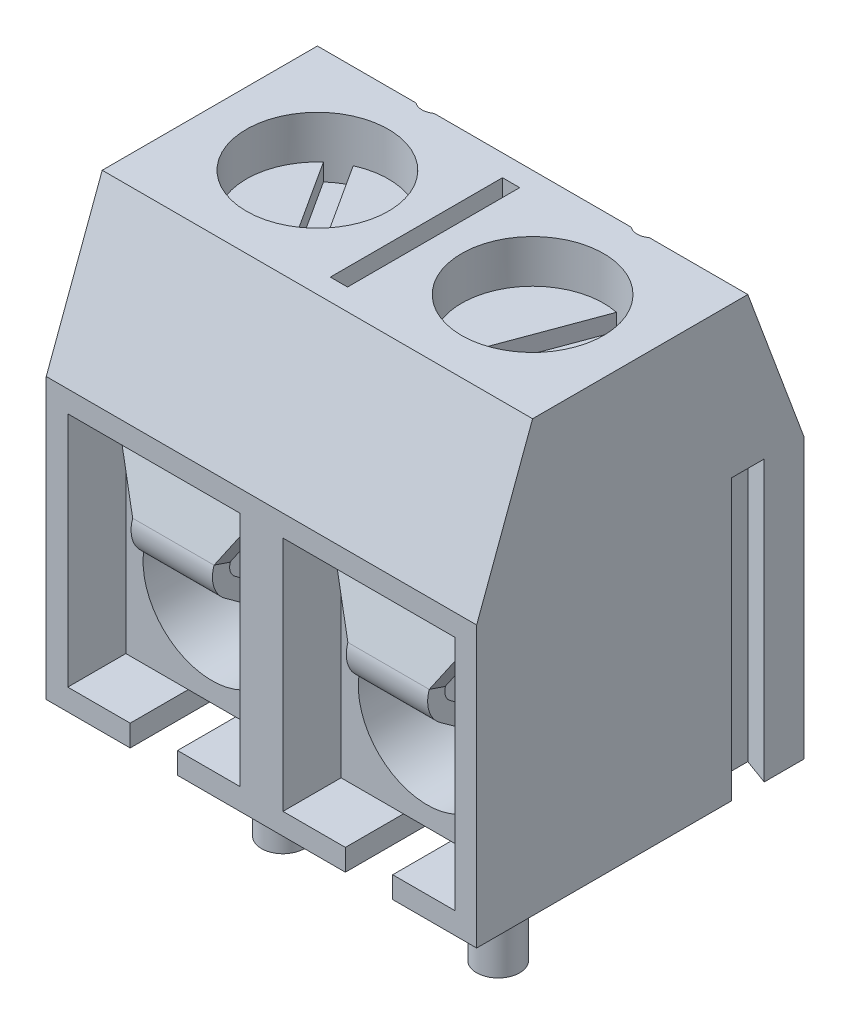
SolidWorks part; units mm, degrees
ref_plane "Front Plane" through (0, 0, 0) normal (0, 0, 1) x (1, 0, 0)
ref_plane "Top Plane" through (0, 0, 0) normal (0, 1, 0) x (1, 0, 0)
ref_plane "Right Plane" through (0, 0, 0) normal (1, 0, 0) x (0, 0, -1)
sketch "Sketch1" plane through (0, 0, 0) normal (0, 1, 0) x (1, 0, 0)
  line L1 (-5, 3.8) -> (5, 3.8)
  line L2 (-5, 3.8) -> (-5, -3.8)
  line L3 (-5, -3.8) -> (5, -3.8)
  line L4 (5, 3.8) -> (5, -3.8)
  dimension "D1" = 10
  dimension "D2" = 5
  dimension "D3" = 7.6
  dimension "D4" = 3.8
extrude "Extrude1" add sketch "Sketch1" along normal blind 10
sketch "Sketch2" plane through (0, 0, 0) normal (1, 0, 0) x (0, 0, -1)
  line L0 (2.5, 10) -> (3.8, 6.5)
  line L1 (3.8, 10) -> (-3.8, 10) construction
  line L2 (3.8, 10) -> (3.8, 0) construction
  line L3 (3.8, 6.5) -> (-3.8, 6.5) construction
  line L4 (-3.8, 10) -> (-3.8, 0) construction
  line L5 (-3.8, 6.5) -> (-2.5, 10)
  line L6 (-2.5, 10) -> (2.5, 10)
  line L7 (3.8, 6.5) -> (3.8, 0)
  line L8 (3.8, 0) -> (-3.8, 0)
  line L9 (-3.8, 0) -> (-3.8, 6.5)
  dimension "D1" = 5
  dimension "D2" = 2.5
  dimension "D3" = 3.5
extrude "Cut-Extrude1" cut sketch "Sketch2" against normal through all and the other way through all flip side to cut
sketch "Sketch3" plane through (0, 10, 0) normal (0, 1, 0) x (-1, 0, 0)
  line L0 (5, -2.5) -> (-5, -2.5) construction
  line L1 (0.2, -2) -> (-0.2, -2)
  line L2 (0.2, -2) -> (0.2, 2)
  line L3 (0.2, 2) -> (-0.2, 2)
  line L4 (-0.2, -2) -> (-0.2, 2)
  circle A0 centre (2.5, 0) radius 1.65
  circle A1 centre (-2.5, 0) radius 1.65
  circle A2 centre (2.5, -2.78) radius 0.35
  circle A3 centre (-2.5, -2.78) radius 0.35
  dimension "D7" = 3.3
  dimension "D8" = 0.7
  dimension "D1" = 0.4
  dimension "D2" = 0.2
  dimension "D3" = 4
  dimension "D4" = 2
  dimension "D5" = 2.5
  dimension "D6" = 2.5
  dimension "D9" = 0.28
extrude "Cut-Extrude2" cut sketch "Sketch3" against normal blind 4
sketch "Sketch4" plane through (0, 0, 3.8) normal (0, 0, 1) x (1, 0, 0)
  line L0 (-5, 6.5) -> (-5, 0) construction
  line L1 (-4.5, 6) -> (-0.5, 6)
  line L2 (-4.5, 6) -> (-4.5, 0.5)
  line L3 (-4.5, 0.5) -> (-0.5, 0.5)
  line L4 (-0.5, 6) -> (-0.5, 0.5)
  line L5 (0.5, 6) -> (4.5, 6)
  line L6 (0.5, 6) -> (0.5, 0.5)
  line L7 (0.5, 0.5) -> (4.5, 0.5)
  line L8 (4.5, 6) -> (4.5, 0.5)
  line L9 (-5, 6.5) -> (5, 6.5) construction
  line L10 (-5, 0) -> (5, 0) construction
  line L11 (5, 6.5) -> (5, 0) construction
  dimension "D1" = 0.5
  dimension "D2" = 0.5
  dimension "D3" = 0.5
  dimension "D4" = 1
  dimension "D5" = 0.5
extrude "Cut-Extrude3" cut sketch "Sketch4" against normal offset from surface (5.6 mm away) 2 up to face at (0, 3.25, -3.8)
sketch "Sketch5" plane through (0, 0, -1.8) normal (0, 0, 1) x (1, 0, 0)
  line L0 (-4.5, 5.6) -> (-0.5, 5.6)
  line L1 (0.5, 5.6) -> (4.5, 5.6)
  line L2 (-4.5, 5.6) -> (-4.5, 0.5)
  line L3 (-0.5, 5.6) -> (-0.5, 6) construction
  line L4 (-4.5, 6) -> (-4.5, 0.5)
  line L5 (-4.5, 0.5) -> (-0.5, 0.5)
  line L6 (-0.5, 0.5) -> (-0.5, 6)
  line L7 (-0.5, 6) -> (-4.5, 6)
  line L8 (-4.5, 6) -> (-4.5, 5.6) construction
  line L9 (-4.5, 0.5) -> (-0.5, 0.5)
  line L10 (-0.5, 0.5) -> (-0.5, 5.6)
  line L11 (-0.5, 6) -> (-4.5, 6) construction
  line L12 (0.5, 6) -> (0.5, 0.5)
  line L13 (0.5, 0.5) -> (4.5, 0.5)
  line L14 (4.5, 0.5) -> (4.5, 6)
  line L15 (4.5, 6) -> (0.5, 6)
  line L16 (0.5, 6) -> (0.5, 5.6) construction
  line L17 (0.5, 0.5) -> (4.5, 0.5)
  line L18 (4.5, 0.5) -> (4.5, 5.6)
  line L19 (4.5, 6) -> (0.5, 6) construction
  line L20 (0.5, 5.6) -> (0.5, 0.5)
  line L21 (4.5, 5.6) -> (4.5, 6) construction
  dimension "D3" = 0.4
  dimension "D1" = 0
  dimension "D2" = 0
extrude "Extrude2" add sketch "Sketch5" along normal offset from surface (4.25 mm away) 1.35 up to face at (2.5, 3.25, 3.8)
sketch "Sketch6" plane through (0, 0, 2.45) normal (0, 0, 1) x (1, 0, 0)
  circle A0 centre (-2.5, 2.5543) radius 1.6
  circle A1 centre (2.5, 2.5543) radius 1.6
  dimension "D1" = 3.2
extrude "Cut-Extrude4" cut sketch "Sketch6" against normal up to surface (4.25 mm away) up to face at (-2.5, 5.8, -1.8)
ref_plane "Plane1" through (-2.5, 0, 0) normal (1, 0, 0) x (0, 0, -1)
ref_plane "Plane2" through (2.5, 0, 0) normal (1, 0, 0) x (0, 0, -1)
sketch "Sketch7" plane through (0, 0, 0) normal (0, 1, 0) x (1, 0, 0)
  line L0 (-5, 2.5) -> (-5, -2.5) construction
  line L1 (-5.6, 3.1) -> (-5, 2.8816)
  line L2 (-5.6, 3.1) -> (-5.6, 1.9)
  line L3 (-5.6, 1.9) -> (-5, 2.1184)
  line L4 (-5, 2.8816) -> (-5, 2.1184)
  line L5 (5, 3.8) -> (-5, 3.8) construction
  dimension "D1" = 1.2
  dimension "D2" = 70
  dimension "D3" = 70
  dimension "D4" = 0.6
  dimension "D5" = 1.9
extrude "Extrude3" add sketch "Sketch7" along normal up to vertex (6.5 mm away) up to point (-5, 6.5, -3.8)
sketch "Sketch9" plane through (0, 0, 0) normal (0, 1, 0) x (1, 0, 0)
  line L0 (5, -3.8) -> (5, 3.8) construction
  line L8 (5, 2.8816) -> (4.4, 3.1)
  line L9 (5, 2.1184) -> (5, 2.8816)
  line L10 (4.4, 1.9) -> (5, 2.1184)
  line L11 (4.4, 3.1) -> (4.4, 1.9)
extrude "Cut-Extrude5" cut sketch "Sketch9" along normal up to vertex (6.5 mm away) up to point (5, 6.5, -3.8)
sketch "Sketch10" plane through (0, 0, 3.8) normal (0, 0, 1) x (1, 0, 0)
  line L0 (-4.5, 0.5) -> (-0.5, 0.5) construction
  line L1 (-3.05, 0.5) -> (-1.95, 0.5)
  line L2 (-3.05, 0.5) -> (-3.05, 0)
  line L3 (-3.05, 0) -> (-1.95, 0)
  line L4 (-1.95, 0.5) -> (-1.95, 0)
  line L5 (-5, 0) -> (5, 0) construction
  line L6 (0.5, 0.5) -> (4.5, 0.5) construction
  line L7 (1.95, 0.5) -> (3.05, 0.5)
  line L8 (1.95, 0.5) -> (1.95, 0)
  line L9 (1.95, 0) -> (3.05, 0)
  line L10 (3.05, 0.5) -> (3.05, 0)
  dimension "D1" = 1.1
  dimension "D2" = 0.55
  dimension "D3" = 0.55
extrude "Cut-Extrude6" cut sketch "Sketch10" against normal blind 3.6
sketch "Sketch11" plane through (0, 0.5, 0) normal (0, -1, 0) x (1, 0, 0)
  line L0 (-2.5, -1.8) -> (-2.5, 2.45) construction
  line L1 (2.5, -1.8) -> (2.5, 2.45) construction
  line L2 (-3.05, 0.2) -> (-1.95, 0.2) construction
  circle A0 centre (-2.5, 0.8) radius 0.5
  circle A1 centre (2.5, 0.8) radius 0.5
  dimension "D1" = 0.6
extrude "Extrude4" add sketch "Sketch11" along normal blind 3.5
sketch "Sketch12" plane through (0, 6, 0) normal (0, -1, 0) x (1, 0, 0)
  circle A0 centre (2.5, 0) radius 1.65 construction
  circle A1 centre (-2.5, 0) radius 1.65 construction
  circle A2 centre (2.5, 0) radius 1.65
  circle A3 centre (-2.5, 0) radius 1.65
extrude "Extrude5" add sketch "Sketch12" against normal offset from surface (3 mm away) 1 up to face at (0, 10, -1.2325)
sketch "Sketch13" plane through (0, 9, 0) normal (0, 1, 0) x (-1, 0, 0)
  line L1 (3.5943, -1.2349) -> (1.8258, 1.506)
  line L2 (3.1742, -1.506) -> (1.4057, 1.2349)
  line L5 (-2.8322, -1.6162) -> (-1.699, 1.4425)
  line L6 (-3.301, -1.4425) -> (-2.1678, 1.6162)
  circle A0 centre (-2.5, 0) radius 1.65 construction
  circle A1 centre (2.5, 0) radius 1.65 construction
  arc A2 (-1.699, 1.4425) -> (-2.1678, 1.6162) centre (-2.5, 0) ccw
  arc A3 (1.8258, 1.506) -> (1.4057, 1.2349) centre (2.5, 0) ccw
  arc A4 (-3.301, -1.4425) -> (-2.8322, -1.6162) centre (-2.5, 0) ccw
  arc A5 (3.1742, -1.506) -> (3.5943, -1.2349) centre (2.5, 0) ccw
  dimension "D1" = 0.5
  dimension "D2" = 0.5
extrude "Cut-Extrude7" cut sketch "Sketch13" against normal blind 0.4
sketch "Sketch14" plane through (-2.5, 0, 0) normal (-1, 0, 0) x (0, 0, 1)
  line L0 (2.45, 5.6) -> (3.0389, 3.8617)
  line L1 (3.0389, 3.8617) -> (0.1672, 1.7876)
  line L2 (0.1672, 1.7876) -> (-0.5464, 2.0974)
  line L3 (-0.5464, 2.0974) -> (-0.7057, 1.7305)
  line L4 (-0.7057, 1.7305) -> (0.2168, 1.33)
  line L5 (0.2168, 1.33) -> (3.5125, 3.7103)
  line L6 (-1.8, 5.6) -> (2.45, 5.6)
  line L7 (2.45, 5.6) -> (2.45, 0.5)
  line L8 (2.45, 0.5) -> (3.8, 0.5)
  line L9 (3.8, 0.5) -> (3.8, 6)
  line L10 (3.8, 6) -> (-1.8, 6)
  line L11 (-1.8, 6) -> (-1.8, 5.6)
  line L12 (-1.8, 5.6) -> (2.45, 5.6)
  line L13 (3.5125, 3.7103) -> (2.7368, 6)
  line L14 (2.7368, 6) -> (-1.8, 6)
  line L17 (-1.8, 6) -> (-1.8, 5.6)
  dimension "D2" = 0.4
  dimension "D3" = 0.4
  dimension "D4" = 0.4
  dimension "D1" = 0
extrude "Extrude6" add sketch "Sketch14" along normal blind 0.945 and the other way blind 0.945
sketch "Sketch15" plane through (0, 1.4494, 4.2784) normal (0, 0.3209, 0.9471) x (1, 0, 0)
  line L2 (-1.555, 4.8) -> (-1.555, 2.904)
  line L3 (-3.445, 4.8) -> (-3.445, 2.904)
  line L4 (-1.555, 2.904) -> (-0.51, 4.8)
  line L5 (-0.51, 4.8) -> (-1.555, 4.8)
  line L6 (-3.445, 2.904) -> (-4.49, 4.8)
  line L8 (-4.49, 4.8) -> (-3.445, 4.8)
extrude "Extrude9" add sketch "Sketch15" against normal blind 0.39
pattern_linear "LPattern1" count 2 spacing 5 along (1, 0, 0) of "Extrude6", "Extrude9"
fillet "Fillet1" radius 0.3 4 edges at (-2.5, 3.8617, 3.0389) (-2.5, 1.7876, 0.1672) (2.5, 1.7876, 0.1672) (2.5, 3.8617, 3.0389)
fillet "Fillet2" radius 0.7 4 edges at (-2.5, 3.7103, 3.5125) (-2.5, 1.33, 0.2168) (2.5, 1.33, 0.2168) (2.5, 3.7103, 3.5125)
sketch "Component_Outline" plane through (0, 0, 0) normal (0, 1, 0) x (1, 0, 0)
  line L0 (5, -3.8) -> (5, 3.8)
  line L1 (5, 3.8) -> (-5, 3.8)
  line L2 (-5, 3.8) -> (-5, 2.8816)
  line L3 (-5, 2.8816) -> (-5.6, 3.1)
  line L4 (-5.6, 3.1) -> (-5.6, 1.9)
  line L5 (-5.6, 1.9) -> (-5, 2.1184)
  line L6 (-5, 2.1184) -> (-5, -3.8)
  line L7 (-5, -3.8) -> (5, -3.8)
